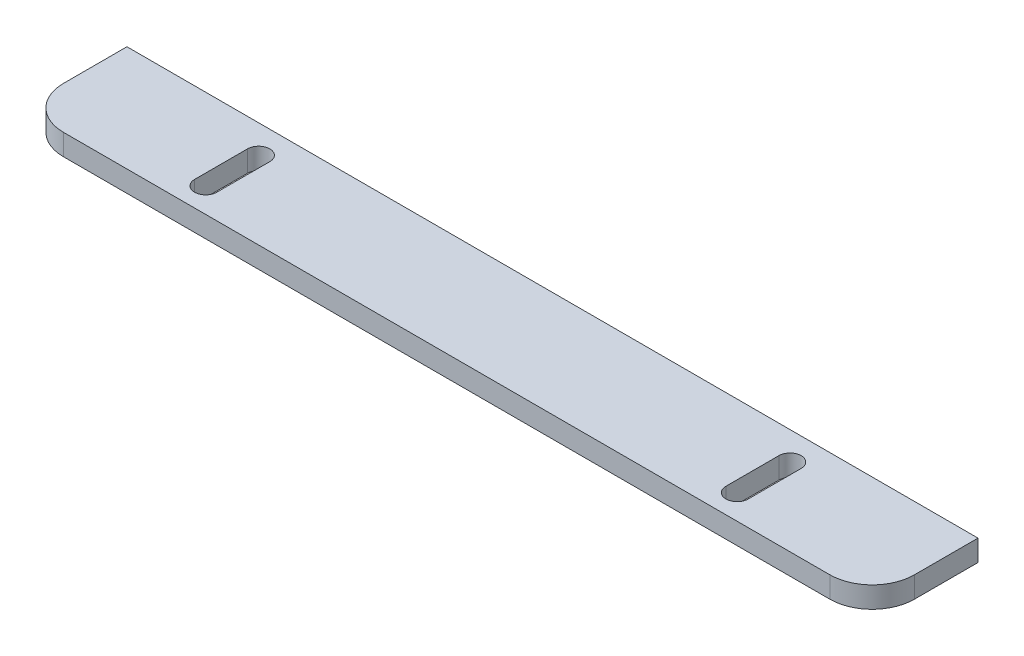
SolidWorks part; units mm, degrees
material "Acrílico (Impacto medio-alto)"
ref_plane "Alzado" through (0, 0, 0) normal (0, 0, 1) x (1, 0, 0)
ref_plane "Planta" through (0, 0, 0) normal (0, 1, 0) x (1, 0, 0)
ref_plane "Vista lateral" through (0, 0, 0) normal (1, 0, 0) x (0, 0, -1)
sketch "Croquis1" plane through (0, 0, 0) normal (0, 1, 0) x (1, 0, 0)
  line L0 (100.5, 25) -> (100.5, 0) construction
  line L1 (10, 0) -> (191, 0)
  line L2 (0, 10) -> (0, 25)
  line L3 (0, 25) -> (201, 25)
  line L4 (201, 10) -> (201, 25)
  line L5 (0, 17.5) -> (201, 17.5) construction
  line L6 (37.75, 25) -> (37.75, 0) construction
  line L7 (37.75, 18.3595) -> (37.75, 5.8595) construction
  line L8 (40.375, 18.3595) -> (40.375, 5.8595)
  line L9 (35.125, 18.3595) -> (35.125, 5.8595)
  line L10 (163.25, 25) -> (163.25, 0) construction
  line L11 (163.25, 18.3595) -> (163.25, 5.8595) construction
  line L12 (160.625, 18.3595) -> (160.625, 5.8595)
  line L13 (165.875, 18.3595) -> (165.875, 5.8595)
  arc A0 (40.375, 18.3595) -> (35.125, 18.3595) centre (37.75, 18.3595) ccw
  arc A1 (35.125, 5.8595) -> (40.375, 5.8595) centre (37.75, 5.8595) ccw
  arc A2 (160.625, 18.3595) -> (165.875, 18.3595) centre (163.25, 18.3595) cw
  arc A3 (165.875, 5.8595) -> (160.625, 5.8595) centre (163.25, 5.8595) cw
  arc A4 (10, 0) -> (0, 10) centre (10, 10) cw
  arc A5 (191, 0) -> (201, 10) centre (191, 10) ccw
  point P13 (37.75, 12.1095)
  point P22 (163.25, 12.1095)
  point P29 (0, 0)
  dimension "D3" = 62.75
  dimension "D6" = 5.8595
  dimension "D4" = 12.5
  dimension "D5" = 5.25
  dimension "D7" = 10
  dimension "D1" = 201
  dimension "D2" = 25
extrude "Saliente-Extruir1" add sketch "Croquis1" along normal blind 5
